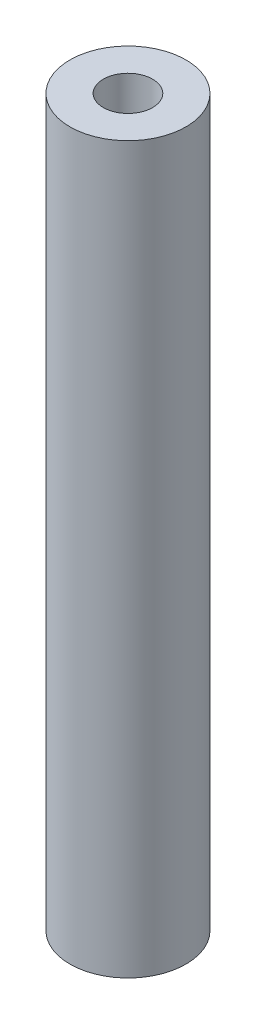
SolidWorks part; units mm, degrees
ref_plane "Front Plane" through (0, 0, 0) normal (0, 0, 1) x (1, 0, 0)
ref_plane "Top Plane" through (0, 0, 0) normal (0, 1, 0) x (1, 0, 0)
ref_plane "Right Plane" through (0, 0, 0) normal (1, 0, 0) x (0, 0, -1)
sketch "Sketch1" plane through (0, 0, 0) normal (0, 1, 0) x (1, 0, 0)
  circle A0 centre (0, 0) radius 40
  circle A1 centre (0, 0) radius 17
  dimension "D1" = 80
  dimension "D2" = 34
extrude "Boss-Extrude1" add sketch "Sketch1" along normal blind 500
